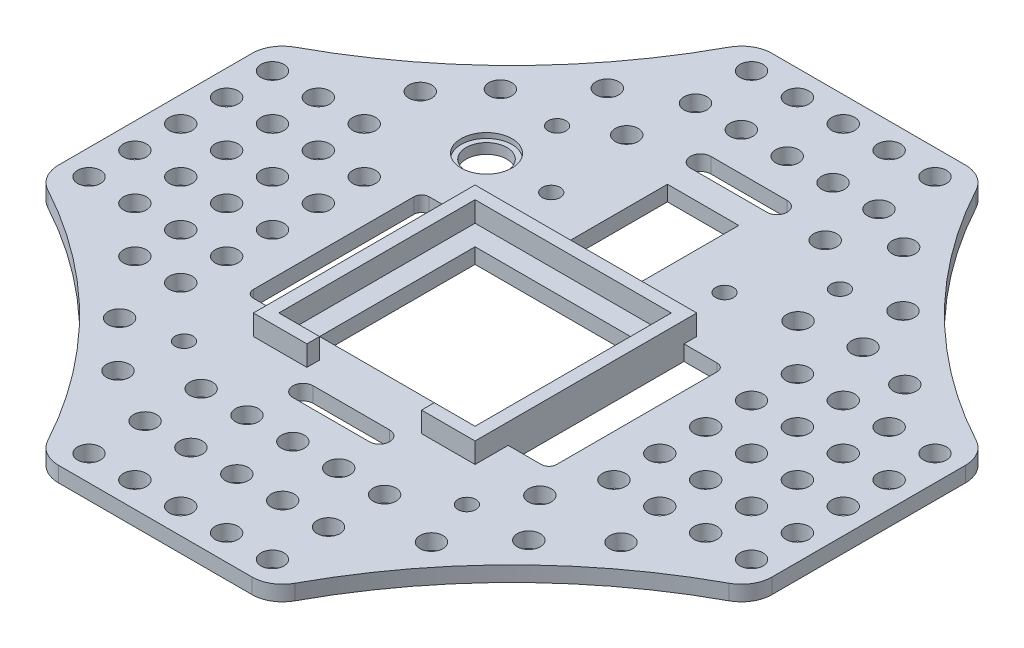
SolidWorks part; units mm, degrees
ref_plane "Front Plane" through (0, 0, 0) normal (0, 0, 1) x (1, 0, 0)
ref_plane "Top Plane" through (0, 0, 0) normal (0, 1, 0) x (1, 0, 0)
ref_plane "Right Plane" through (0, 0, 0) normal (1, 0, 0) x (0, 0, -1)
sketch "Sketch1" plane through (0, 0, 0) normal (0, 1, 0) x (1, 0, 0)
  line L0 (-32, 0) -> (32, 0) construction
  line L1 (-32, 41) -> (32, 41)
  line L2 (-32, 41) -> (-32, -41)
  line L3 (-32, -41) -> (32, -41)
  line L4 (32, 41) -> (32, -41)
  line L5 (-32, 41) -> (32, -41) construction
  line L6 (-32, -41) -> (32, 41) construction
  line L7 (0, 41) -> (0, -41) construction
  circle A0 centre (27.75, -36.6) radius 1.75
  circle A1 centre (-27.75, -36.6) radius 1.75
  circle A2 centre (27.75, 36.6) radius 1.75
  circle A3 centre (-27.75, 36.6) radius 1.75
  point P0 (0, 0)
  dimension "D3" = 3.5
  dimension "D1" = 64
  dimension "D2" = 82
  dimension "D4" = 27.75
  dimension "D5" = 36.6
extrude "Boss-Extrude1" add sketch "Sketch1" along normal blind 3
sketch "Sketch2" plane through (0, 3, 0) normal (0, 1, 0) x (1, 0, 0)
  line L0 (0, 41) -> (0, -41) construction
  line L1 (32, 41) -> (-32, 41) construction
  line L2 (-32, -41) -> (32, -41) construction
  line L3 (-32, 0) -> (32, 0) construction
  line L4 (-32, 41) -> (-32, -41) construction
  line L5 (32, -41) -> (32, 41) construction
  line L6 (-11.25, -26.5) -> (-11.25, -29)
  line L7 (-19.25, 12) -> (19.25, 12)
  line L8 (-19.25, 12) -> (-19.25, -26.5)
  line L9 (-19.25, -26.5) -> (-11.25, -26.5)
  line L10 (19.25, 12) -> (19.25, -26.5)
  line L11 (-19.25, 12) -> (19.25, -26.5) construction
  line L12 (-19.25, -26.5) -> (19.25, 12) construction
  line L13 (-21.75, 14.5) -> (21.75, 14.5)
  line L14 (-21.75, 14.5) -> (-21.75, -29)
  line L15 (-21.75, -29) -> (-11.25, -29)
  line L16 (21.75, 14.5) -> (21.75, -29)
  line L17 (-21.75, 14.5) -> (21.75, -29) construction
  line L18 (-21.75, -29) -> (21.75, 14.5) construction
  line L19 (11.25, -26.5) -> (11.25, -29)
  line L20 (11.25, -26.5) -> (19.25, -26.5)
  line L21 (11.25, -29) -> (21.75, -29)
  point P12 (0, -7.25)
  point P17 (0, -7.25)
  point P19 (0, -7.25)
  dimension "D1" = 38.5
  dimension "D2" = 2.5
  dimension "D3" = 12
  dimension "D4" = 8
  dimension "D5" = 8
extrude "GPS-Housing" add sketch "Sketch2" along normal blind 4
sketch "Sketch3" plane through (0, 3, 0) normal (0, 1, 0) x (1, 0, 0)
  line L0 (-32, 24.7) -> (32, 24.7) construction
  line L1 (-32, 41) -> (-32, -41) construction
  line L2 (32, -41) -> (32, 41) construction
  line L3 (0, 41) -> (0, 6.6316) construction
  line L6 (21.75, 14.5) -> (-21.75, 14.5) construction
  line L7 (32, 41) -> (-32, 41) construction
  circle A0 centre (-17, 24.7) radius 1.75
  circle A1 centre (17, 24.7) radius 1.75
  dimension "D1" = 3.5
  dimension "D2" = 10.2
  dimension "D3" = 17
extrude "Spectrum-Cover-Hole" cut sketch "Sketch3" against normal through all
sketch "Sketch4" plane through (0, 3, 0) normal (0, 1, 0) x (1, 0, 0)
  line L0 (-21.75, 14.5) -> (-21.75, -29) construction
  line L3 (-21.75, 12) -> (-28.25, 12)
  line L4 (-21.75, 12) -> (-21.75, -22.5)
  line L5 (-21.75, -22.5) -> (-28.25, -22.5)
  line L6 (-29.75, 10.5) -> (-29.75, -21)
  line L10 (0, 41) -> (0, -41) construction
  line L11 (32, 41) -> (-32, 41) construction
  line L12 (-32, -41) -> (32, -41) construction
  line L14 (-19.25, 12) -> (19.25, 12) construction
  line L15 (-11.25, -26.5) -> (-19.25, -26.5) construction
  line L16 (29.75, 10.5) -> (29.75, -21)
  line L17 (21.75, -22.5) -> (28.25, -22.5)
  line L18 (21.75, 12) -> (21.75, -22.5)
  line L19 (21.75, 12) -> (28.25, 12)
  arc A0 (-28.25, -22.5) -> (-29.75, -21) centre (-28.25, -21) cw
  arc A1 (-28.25, 12) -> (-29.75, 10.5) centre (-28.25, 10.5) ccw
  arc A2 (28.25, 12) -> (29.75, 10.5) centre (28.25, 10.5) cw
  arc A3 (28.25, -22.5) -> (29.75, -21) centre (28.25, -21) ccw
  dimension "D3" = 1.5
  dimension "D1" = 8
  dimension "D2" = 4
extrude "Tape-Slot" cut sketch "Sketch4" against normal through all
sketch "Sketch6" plane through (0, 3, 0) normal (0, 1, 0) x (1, 0, 0)
  line L0 (0, 41) -> (0, -41) construction
  line L1 (32, 41) -> (-32, 41) construction
  line L2 (-32, -41) -> (32, -41) construction
  line L3 (-32, 0) -> (32, 0) construction
  line L4 (-32, 41) -> (-32, -41) construction
  line L5 (32, -41) -> (32, 41) construction
  line L6 (0, 0) -> (116.6726, -116.6726) construction
  line L7 (0, -41) -> (0, -155.7646) construction
  line L8 (32, 0) -> (119.0429, 0) construction
  line L9 (70, 22.6159) -> (70, -22.6159)
  line L10 (-22.6159, -70) -> (22.6159, -70)
  line L11 (-70, 22.6159) -> (-70, -22.6159)
  line L12 (-22.6159, 70) -> (22.6159, 70)
  line L14 (-32, 41) -> (32, 41)
  line L15 (32, 41) -> (32, -41)
  line L16 (32, -41) -> (-32, -41)
  line L17 (-32, -41) -> (-32, 41)
  arc A0 (70, -22.6159) -> (22.6159, -70) centre (116.6726, -116.6726) ccw
  circle A1 centre (116.6726, -116.6726) radius 105 construction
  arc A2 (-70, -22.6159) -> (-22.6159, -70) centre (-116.6726, -116.6726) cw
  arc A3 (70, 22.6159) -> (22.6159, 70) centre (116.6726, 116.6726) cw
  arc A4 (-70, 22.6159) -> (-22.6159, 70) centre (-116.6726, 116.6726) ccw
  point P24 (0, -70)
  point P28 (116.6726, -116.6726)
  point P30 (70, 0)
  point P36 (-70, 0)
  dimension "D9" = 210
  dimension "D1" = 45
  dimension "D2" = 70
  dimension "D3" = 70
  dimension "D4" = 165
extrude "Extension" add sketch "Sketch6" against normal blind 3
sketch "Sketch7" plane through (0, 3, 0) normal (0, 1, 0) x (1, 0, 0)
  line L0 (0, 70) -> (0, -70) construction
  line L1 (22.6159, 70) -> (-22.6159, 70) construction
  line L2 (-22.6159, -70) -> (22.6159, -70) construction
  line L3 (-70, 0) -> (70, 0) construction
  line L4 (-70, 22.6159) -> (-70, -22.6159) construction
  line L5 (70, -22.6159) -> (70, 22.6159) construction
  circle A0 centre (-30, 25) radius 4
  dimension "D1" = 8
  dimension "D2" = 30
  dimension "D3" = 25
extrude "Arm-Button-Hole" cut sketch "Sketch7" against normal through all
sketch "Sketch8" plane through (0, 3, 0) normal (0, 1, 0) x (1, 0, 0)
  circle A0 centre (-30, 25) radius 5
  circle A1 centre (-30, 25) radius 4 construction
  dimension "D1" = 10
extrude "Cut-Extrude4" cut sketch "Sketch8" against normal blind 1
sketch "Sketch9" plane through (0, 3, 0) normal (0, 1, 0) x (1, 0, 0)
  line L0 (-70, 0) -> (70, 0) construction
  line L1 (-70, 22.6159) -> (-70, -22.6159) construction
  line L2 (70, -22.6159) -> (70, 22.6159) construction
  line L3 (-7.5, 44.5) -> (7.5, 44.5) construction
  line L4 (-7.5, 46.5) -> (7.5, 46.5)
  line L5 (-7.5, 42.5) -> (7.5, 42.5)
  line L6 (21.75, 14.5) -> (-21.75, 14.5) construction
  line L7 (0, 0) -> (0, 70) construction
  line L8 (22.6159, 70) -> (-22.6159, 70) construction
  line L9 (-7.5, -33.5) -> (7.5, -33.5) construction
  line L10 (-7.5, -31.5) -> (7.5, -31.5)
  line L11 (-7.5, -35.5) -> (7.5, -35.5)
  line L12 (-11.25, -26.5) -> (-19.25, -26.5) construction
  arc A0 (-7.5, 46.5) -> (-7.5, 42.5) centre (-7.5, 44.5) ccw
  arc A1 (7.5, 42.5) -> (7.5, 46.5) centre (7.5, 44.5) ccw
  arc A2 (-7.5, -31.5) -> (-7.5, -35.5) centre (-7.5, -33.5) ccw
  arc A3 (7.5, -35.5) -> (7.5, -31.5) centre (7.5, -33.5) ccw
  point P8 (0, 44.5)
  point P21 (0, -33.5)
  point P27 (0, -31.5)
  dimension "D1" = 30
  dimension "D2" = 4
  dimension "D3" = 15
  dimension "D4" = 5
  dimension "D5" = 4
  dimension "D6" = 15
extrude "Wire-Slot" cut sketch "Sketch9" against normal through all
sketch "Sketch10" plane through (0, 3, 0) normal (0, 1, 0) x (1, 0, 0)
  line L0 (-70, 0) -> (70, 0) construction
  line L1 (-70, 22.6159) -> (-70, -22.6159) construction
  line L2 (70, -22.6159) -> (70, 22.6159) construction
  line L3 (0, 70) -> (0, -70) construction
  line L4 (22.6159, 70) -> (-22.6159, 70) construction
  line L5 (-22.6159, -70) -> (22.6159, -70) construction
  circle A0 centre (-65, 18) radius 2.25
  circle A1 centre (-56, 18) radius 2.25
  circle A2 centre (-47, 18) radius 2.25
  circle A3 centre (-47, -27) radius 2.25
  circle A4 centre (-56, 9) radius 2.25
  circle A5 centre (-47, 9) radius 2.25
  circle A6 centre (-38, 9) radius 2.25
  circle A7 centre (-56, 0) radius 2.25
  circle A8 centre (-47, 0) radius 2.25
  circle A9 centre (-38, 0) radius 2.25
  circle A10 centre (-56, -9) radius 2.25
  circle A11 centre (-47, -9) radius 2.25
  circle A12 centre (-38, -9) radius 2.25
  circle A13 centre (-56, -18) radius 2.25
  circle A14 centre (-47, -18) radius 2.25
  circle A15 centre (-38, -18) radius 2.25
  circle A16 centre (-65, 9) radius 2.25
  circle A17 centre (-65, 0) radius 2.25
  circle A18 centre (-65, -9) radius 2.25
  circle A19 centre (-65, -18) radius 2.25
  circle A20 centre (65, -18) radius 2.25
  circle A21 centre (65, -9) radius 2.25
  circle A22 centre (65, 0) radius 2.25
  circle A23 centre (65, 9) radius 2.25
  circle A24 centre (38, -18) radius 2.25
  circle A25 centre (47, -18) radius 2.25
  circle A26 centre (56, -18) radius 2.25
  circle A27 centre (38, -9) radius 2.25
  circle A28 centre (47, -9) radius 2.25
  circle A29 centre (56, -9) radius 2.25
  circle A30 centre (38, 0) radius 2.25
  circle A31 centre (47, 0) radius 2.25
  circle A32 centre (56, 0) radius 2.25
  circle A33 centre (38, 9) radius 2.25
  circle A34 centre (47, 9) radius 2.25
  circle A35 centre (56, 9) radius 2.25
  circle A36 centre (38, 18) radius 2.25
  circle A37 centre (47, 18) radius 2.25
  circle A38 centre (56, 18) radius 2.25
  circle A39 centre (65, 18) radius 2.25
  circle A40 centre (-18, 65) radius 2.25
  circle A41 centre (-18, 54) radius 2.25
  circle A42 centre (0, -65) radius 2.25
  circle A43 centre (-9, 65) radius 2.25
  circle A44 centre (-9, 54) radius 2.25
  circle A45 centre (0, 65) radius 2.25
  circle A46 centre (0, -54) radius 2.25
  circle A47 centre (0, 54) radius 2.25
  circle A48 centre (9, 65) radius 2.25
  circle A49 centre (9, 54) radius 2.25
  circle A50 centre (0, -43) radius 2.25
  circle A51 centre (18, 54) radius 2.25
  circle A52 centre (18, 65) radius 2.25
  circle A53 centre (-38, -27) radius 2.25
  circle A54 centre (-38, -39) radius 2.25
  circle A55 centre (18, -43) radius 2.25
  circle A56 centre (18, -54) radius 2.25
  circle A57 centre (-18, -43) radius 2.25
  circle A58 centre (-9, -43) radius 2.25
  circle A59 centre (9, -43) radius 2.25
  circle A60 centre (-18, -54) radius 2.25
  circle A61 centre (-9, -54) radius 2.25
  circle A62 centre (9, -54) radius 2.25
  circle A63 centre (-18, -65) radius 2.25
  circle A64 centre (-9, -65) radius 2.25
  circle A65 centre (9, -65) radius 2.25
  circle A66 centre (18, -65) radius 2.25
  circle A67 centre (-38, 18) radius 2.25 [skipped]
  circle A68 centre (-47, 29) radius 2.25
  circle A69 centre (-29.1998, -48.1121) radius 2.25
  circle A70 centre (29.0554, 27.0772) radius 2.25
  circle A71 centre (39.8891, 29) radius 2.25
  circle A72 centre (37.6391, 39.0789) radius 2.25
  circle A73 centre (50.3305, 26.75) radius 2.25
  circle A74 centre (-29.1998, 47.9048) radius 2.25
  circle A75 centre (26.8816, 49.9671) radius 2.25
  circle A76 centre (33.351, -27.8903) radius 2.25
  circle A77 centre (49.2828, -27.8903) radius 2.25
  circle A78 centre (30.6541, -46.4637) radius 2.25
  circle A79 centre (39.8891, -36.5947) radius 2.25
  circle A80 centre (-19.366, 41.8778) radius 2.25
  circle A81 centre (18, 43.4589) radius 2.25
  circle A82 centre (-39.5411, 37.262) radius 2.25
  dimension "D1" = 4.5
  dimension "D6" = 4.5
  dimension "D9" = 4.5
  dimension "D12" = 4.5
  dimension "D14" = 4.5
  dimension "D16" = 4.5
  dimension "D2" = 65
  dimension "D3" = 18
  dimension "D7" = 18
  dimension "D8" = 65
  dimension "D10" = 9
  dimension "D11" = 9
  dimension "D13" = 12
  dimension "D15" = 11
  dimension "D4" = 4
  dimension "D5" = 5
extrude "Markers-Hole" cut sketch "Sketch10" against normal through all
fillet "Fillet1" radius 6 8 edges at (22.6159, 1.5, -70) (70, 1.5, -22.6159) (70, 1.5, 22.6159) (22.6159, 1.5, 70) (-22.6159, 1.5, 70) (-70, 1.5, 22.6159) (-70, 1.5, -22.6159) (-22.6159, 1.5, -70)
sketch "Sketch11" plane through (0, 3, 0) normal (0, 1, 0) x (1, 0, 0)
  line L0 (-19.25, -26.5) -> (-19.25, 12) construction
  line L1 (-15.25, 8) -> (15.25, 8)
  line L2 (-15.25, 8) -> (-15.25, -22.5)
  line L3 (-15.25, -22.5) -> (15.25, -22.5)
  line L4 (15.25, 8) -> (15.25, -22.5)
  line L5 (19.25, 12) -> (19.25, -26.5) construction
  line L6 (-19.25, 12) -> (19.25, 12) construction
  line L7 (-11.25, -26.5) -> (-19.25, -26.5) construction
  line L8 (0, 70) -> (0, -70) construction
  line L9 (18.9659, 70) -> (-18.9659, 70) construction
  line L10 (-18.9659, -70) -> (18.9659, -70) construction
  line L11 (21.75, 14.5) -> (-21.75, 14.5) construction
  line L12 (-7, 37.5) -> (7, 37.5)
  line L13 (-7, 37.5) -> (-7, 18.5)
  line L14 (-7, 18.5) -> (7, 18.5)
  line L15 (7, 37.5) -> (7, 18.5)
  line L16 (-7.5, 42.5) -> (7.5, 42.5) construction
  dimension "D1" = 4
  dimension "D2" = 4
  dimension "D3" = 4
  dimension "D4" = 4
  dimension "D5" = 4
  dimension "D6" = 5
  dimension "D7" = 7
  dimension "D8" = 7
extrude "Weight-Reducer" cut sketch "Sketch11" against normal through all
